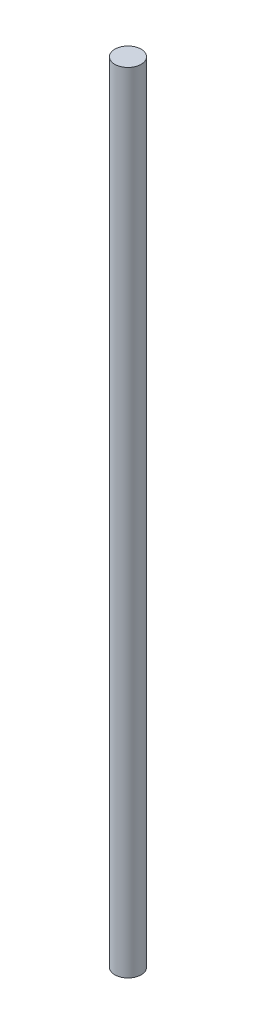
SolidWorks part; units mm, degrees
ref_plane "前视基准面" through (0, 0, 0) normal (0, 0, 1) x (1, 0, 0)
ref_plane "上视基准面" through (0, 0, 0) normal (0, 1, 0) x (1, 0, 0)
ref_plane "右视基准面" through (0, 0, 0) normal (1, 0, 0) x (0, 0, -1)
sketch "Sketch1" plane through (0, 0, 0) normal (0, 1, 0) x (1, 0, 0)
  circle A0 centre (0, 0) radius 5
  dimension "D1" = 10
extrude "Extrude1" add sketch "Sketch1" along normal blind 300
